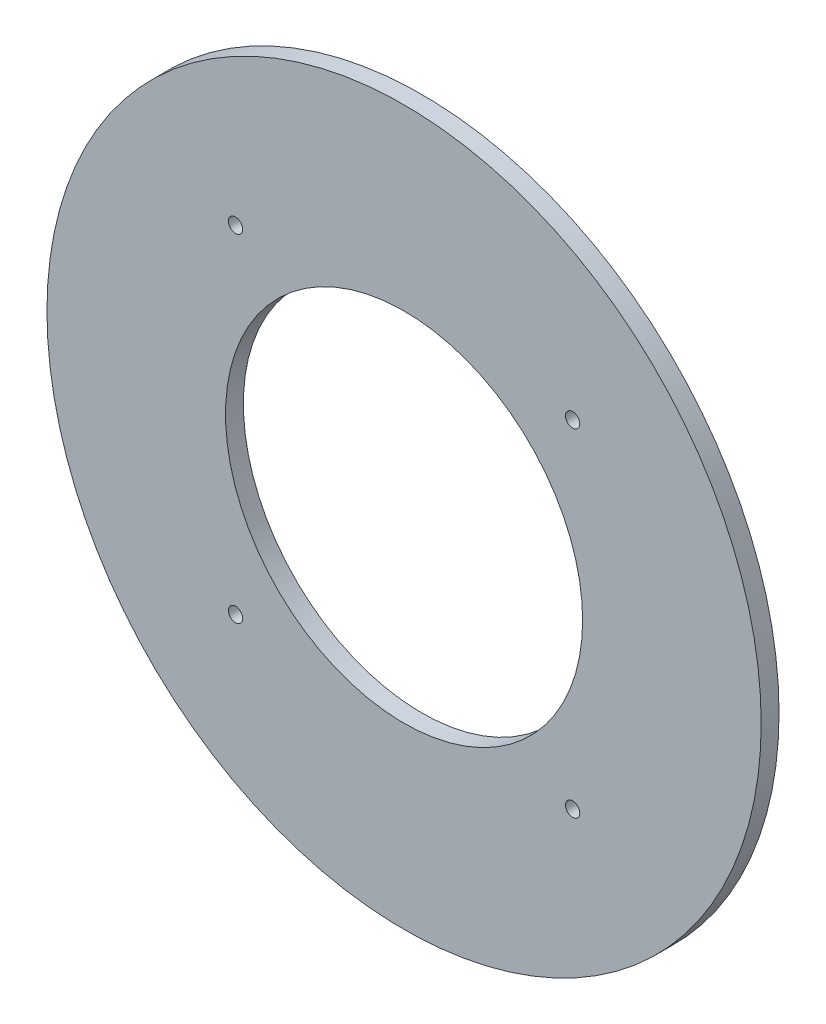
SolidWorks part; units mm, degrees
material "Pine"
ref_plane "Front Plane" through (0, 0, 0) normal (0, 0, 1) x (1, 0, 0)
ref_plane "Top Plane" through (0, 0, 0) normal (0, 1, 0) x (1, 0, 0)
ref_plane "Right Plane" through (0, 0, 0) normal (1, 0, 0) x (0, 0, -1)
sketch "Sketch1" plane through (0, 0, 0) normal (0, 0, 1) x (1, 0, 0)
  circle A0 centre (0, 0) radius 63.5
  circle A1 centre (0, 0) radius 127
  circle A2 centre (-59.944, 59.944) radius 2.54 construction
  circle A3 centre (-59.944, 59.944) radius 2.54
  circle A4 centre (59.944, 59.944) radius 2.54 construction
  circle A5 centre (59.944, 59.944) radius 2.54
  circle A6 centre (-59.944, -59.944) radius 2.54 construction
  circle A7 centre (59.944, -59.944) radius 2.54 construction
  circle A8 centre (-59.944, -59.944) radius 2.54
  circle A9 centre (59.944, -59.944) radius 2.54
  dimension "D1" = 127
  dimension "D2" = 254
extrude "Boss-Extrude1" add sketch "Sketch1" along normal blind 6.35
